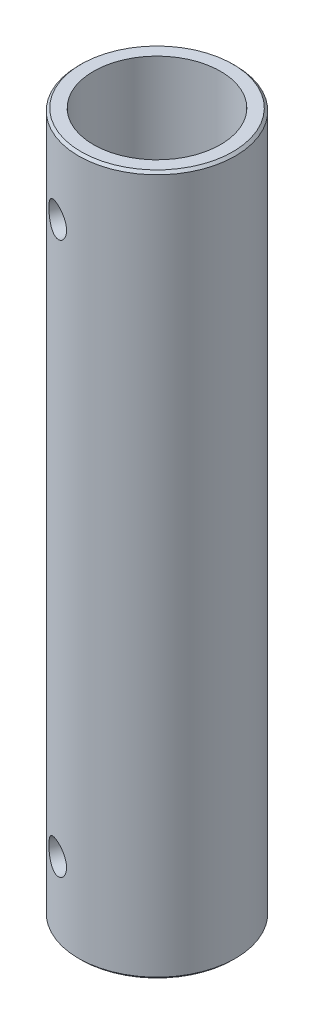
SolidWorks part; units mm, degrees
ref_plane "Front Plane" through (0, 0, 0) normal (0, 0, 1) x (1, 0, 0)
ref_plane "Top Plane" through (0, 0, 0) normal (0, 1, 0) x (1, 0, 0)
ref_plane "Right Plane" through (0, 0, 0) normal (1, 0, 0) x (0, 0, -1)
sketch "Sketch1" plane through (0, 0, 0) normal (0, 1, 0) x (1, 0, 0)
  circle A0 centre (0, 0) radius 7.94
  circle A1 centre (0, 0) radius 6.44
  dimension "D1" = 15.88
  dimension "D2" = 1.5
extrude "Boss-Extrude1" add sketch "Sketch1" along normal blind 70.91
chamfer "Chamfer1" distance 0.25 angle 45 2 edges at (0, 0, 7.94) (0, 70.91, 7.94)
sketch "Sketch2" plane through (-2.0935, 0, 5.4626) normal (-0.3579, 0, 0.9338) x (0.9338, 0, 0.3579)
  circle A0 centre (0, 63.41) radius 1.55 construction
  circle A1 centre (0, 63.41) radius 1.55
  circle A2 centre (0, 7.5) radius 1.55 construction
  circle A3 centre (0, 7.5) radius 1.55
extrude "Cut-Extrude1" cut sketch "Sketch2" against normal through all both and the other way through all
